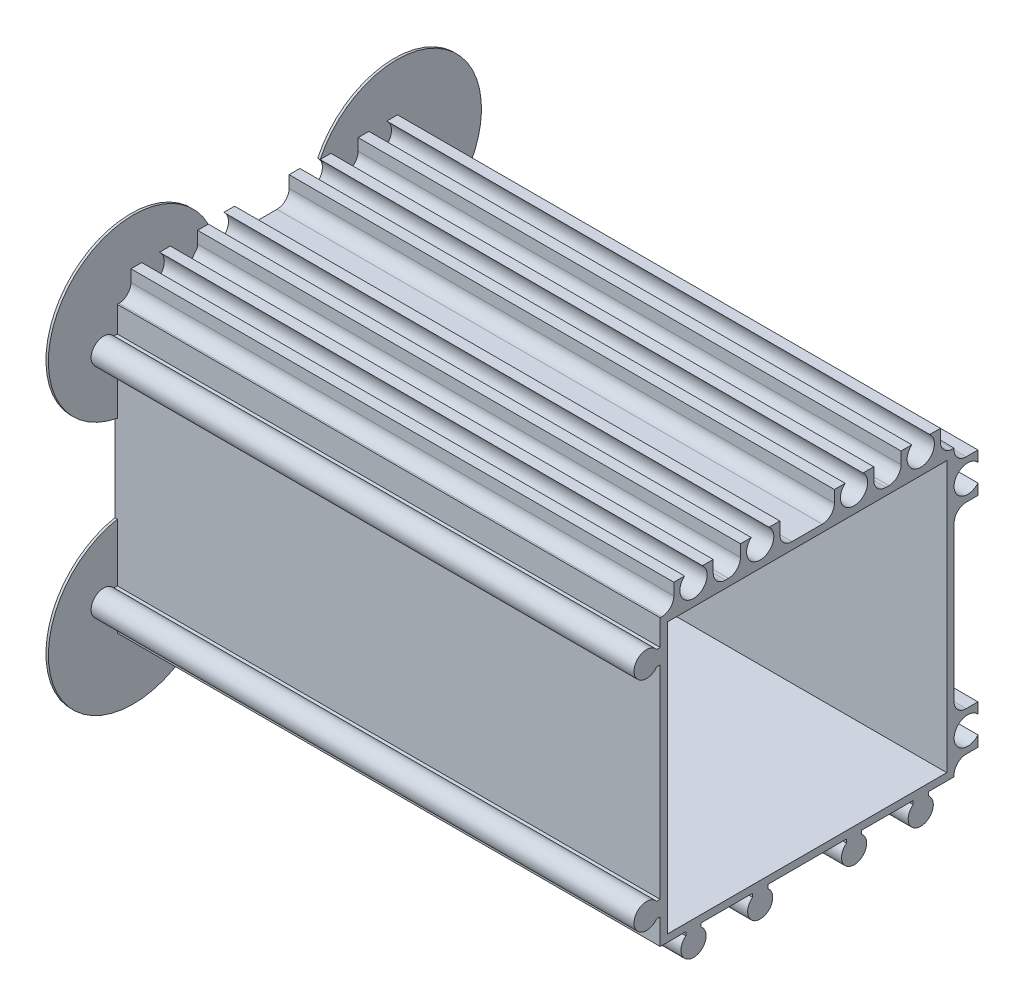
SolidWorks part; units mm, degrees
ref_plane "Спереди" through (0, 0, 0) normal (0, 0, 1) x (1, 0, 0)
ref_plane "Сверху" through (0, 0, 0) normal (0, 1, 0) x (1, 0, 0)
ref_plane "Справа" through (0, 0, 0) normal (1, 0, 0) x (0, 0, -1)
ref_plane "Плоскость4" through (90, 0, 0) normal (1, 0, 0) x (0, 0, -1)
sketch "Эскиз1" plane through (90, 0, 0) normal (1, 0, 0) x (0, 0, -1)
  line L0 (6.75, 160.9062) -> (6.75, 204.25)
  line L1 (6.75, 204.25) -> (-38.0938, 204.25)
  line L2 (-38.0938, 201.75) -> (-37.5, 201.75)
  line L3 (-37.5, 201.75) -> (-37.5, 168.25)
  line L4 (-37.5, 168.25) -> (-38.0938, 168.25)
  line L5 (-38.0938, 165.75) -> (-37.5, 165.75)
  line L6 (-37.5, 165.75) -> (-37.5, 161.5)
  line L7 (-37.5, 161.5) -> (-33.25, 161.5)
  line L8 (-33.25, 161.5) -> (-33.25, 160.9062)
  line L9 (-30.75, 160.9062) -> (-30.75, 161.5)
  line L10 (-30.75, 161.5) -> (-22.25, 161.5)
  line L11 (-22.25, 161.5) -> (-22.25, 160.9062)
  line L12 (-19.75, 160.9062) -> (-19.75, 161.5)
  line L13 (-19.75, 161.5) -> (-6.75, 161.5)
  line L14 (-6.75, 161.5) -> (-6.75, 160.9062)
  line L15 (-4.25, 160.9062) -> (-4.25, 161.5)
  line L16 (-4.25, 161.5) -> (4.25, 161.5)
  line L17 (4.25, 161.5) -> (4.25, 160.9062)
  arc A0 (-38.0938, 204.25) -> (-38.0938, 201.75) centre (-39.75, 203) ccw
  arc A1 (-38.0938, 168.25) -> (-38.0938, 165.75) centre (-39.75, 167) ccw
  arc A2 (-33.25, 160.9062) -> (-30.75, 160.9062) centre (-32, 159.25) ccw
  arc A3 (-22.25, 160.9062) -> (-19.75, 160.9062) centre (-21, 159.25) ccw
  arc A4 (-6.75, 160.9062) -> (-4.25, 160.9062) centre (-5.5, 159.25) ccw
  arc A5 (4.25, 160.9062) -> (6.75, 160.9062) centre (5.5, 159.25) ccw
extrude "Бобышка-Вытянуть1" add sketch "Эскиз1" against normal blind 90
sketch "Эскиз2" plane through (0, 0, -6.75) normal (0, 0, -1) x (-1, 0, 0)
  line L0 (0, 204.25) -> (0, 161.5)
  line L1 (0, 161.5) -> (-90, 161.5)
  line L2 (-90, 161.5) -> (-90, 204.25)
  line L3 (-90, 204.25) -> (0, 204.25)
extrude "Бобышка-Вытянуть2" add sketch "Эскиз2" along normal blind 8.2
sketch "Эскиз3" plane through (0, 204.25, 0) normal (0, 1, 0) x (-1, 0, 0)
  line L0 (-90, -14.95) -> (-90, 37.5)
  line L1 (-90, 37.5) -> (0, 37.5)
  line L2 (0, 37.5) -> (0, -14.95)
  line L3 (0, -14.95) -> (-90, -14.95)
extrude "Бобышка-Вытянуть3" add sketch "Эскиз3" along normal blind 8.2
sketch "Эскиз4" plane through (0, 0, 0) normal (-1, 0, 0) x (0, 0, 1)
  line L0 (-14.95, 161.5) -> (-11, 161.5)
  line L1 (-11, 161.5) -> (-11, 163.75)
  line L2 (-11, 163.75) -> (-14.95, 163.75)
  line L3 (-14.95, 163.75) -> (-14.95, 161.5)
extrude "Вырез-Вытянуть1" cut sketch "Эскиз4" against normal through all
sketch "Эскиз5" plane through (0, 0, 0) normal (-1, 0, 0) x (0, 0, 1)
  line L0 (-14.95, 170.25) -> (-11, 170.25)
  line L1 (-11, 170.25) -> (-11, 199.75)
  line L2 (-11, 199.75) -> (-14.95, 199.75)
  line L3 (-14.95, 199.75) -> (-14.95, 170.25)
extrude "Вырез-Вытянуть2" cut sketch "Эскиз5" against normal through all
sketch "Эскиз6" plane through (0, 0, 0) normal (-1, 0, 0) x (0, 0, 1)
  line L0 (-14.95, 212.45) -> (-14.95, 206.25)
  line L1 (-14.95, 206.25) -> (-11, 206.25)
  line L2 (-11, 206.25) -> (-11, 212.45)
  line L3 (-11, 212.45) -> (-14.95, 212.45)
extrude "Вырез-Вытянуть3" cut sketch "Эскиз6" against normal through all
sketch "Эскиз7" plane through (0, 0, 0) normal (-1, 0, 0) x (0, 0, 1)
  line L0 (-11, 212.45) -> (-11, 208.5)
  line L1 (-11, 208.5) -> (-8.75, 208.5)
  line L2 (-8.75, 208.5) -> (-8.75, 212.45)
  line L3 (-8.75, 212.45) -> (-11, 212.45)
extrude "Вырез-Вытянуть4" cut sketch "Эскиз7" against normal through all
sketch "Эскиз8" plane through (0, 0, 0) normal (-1, 0, 0) x (0, 0, 1)
  line L0 (-2.25, 212.45) -> (-2.25, 208.5)
  line L1 (-2.25, 208.5) -> (2.25, 208.5)
  line L2 (2.25, 208.5) -> (2.25, 212.45)
  line L3 (2.25, 212.45) -> (-2.25, 212.45)
extrude "Вырез-Вытянуть5" cut sketch "Эскиз8" against normal through all
sketch "Эскиз9" plane through (0, 0, 0) normal (-1, 0, 0) x (0, 0, 1)
  line L0 (8.75, 212.45) -> (8.75, 208.5)
  line L1 (8.75, 208.5) -> (17.75, 208.5)
  line L2 (17.75, 208.5) -> (17.75, 212.45)
  line L3 (17.75, 212.45) -> (8.75, 212.45)
extrude "Вырез-Вытянуть6" cut sketch "Эскиз9" against normal through all
sketch "Эскиз10" plane through (0, 0, 0) normal (-1, 0, 0) x (0, 0, 1)
  line L0 (24.25, 212.45) -> (24.25, 208.5)
  line L1 (24.25, 208.5) -> (28.75, 208.5)
  line L2 (28.75, 208.5) -> (28.75, 212.45)
  line L3 (28.75, 212.45) -> (24.25, 212.45)
extrude "Вырез-Вытянуть7" cut sketch "Эскиз10" against normal through all
sketch "Эскиз11" plane through (0, 0, 0) normal (-1, 0, 0) x (0, 0, 1)
  line L0 (37.5, 212.45) -> (35.25, 212.45)
  line L1 (35.25, 212.45) -> (35.25, 208.5)
  line L2 (35.25, 208.5) -> (37.5, 208.5)
  line L3 (37.5, 208.5) -> (37.5, 212.45)
extrude "Вырез-Вытянуть8" cut sketch "Эскиз11" against normal through all
sketch "Эскиз12" plane through (90, 0, 0) normal (1, 0, 0) x (0, 0, -1)
  line L0 (9.8, 207.3) -> (-36.3, 207.3)
  line L1 (-36.3, 207.3) -> (-36.3, 162.7)
  line L2 (-36.3, 162.7) -> (9.8, 162.7)
  line L3 (9.8, 162.7) -> (9.8, 207.3)
  line L4 (11, 170.25) -> (11, 199.75) construction
  line L5 (-37.5, 201.75) -> (-37.5, 168.25) construction
  line L6 (-8.75, 208.5) -> (-17.75, 208.5) construction
  line L7 (-19.75, 161.5) -> (-6.75, 161.5) construction
  dimension "D1" = 1.2
  dimension "D2" = 1.2
  dimension "D3" = 1.2
  dimension "D4" = 1.2
extrude "Вырез-Вытянуть9" cut sketch "Эскиз12" against normal blind 86.2
hole_wizard "Диаметр отверстия Ø2.5 (2.5)1" positions "Эскиз14" profile "Эскиз13" hole size "Ø2.5" standard "Ansi Metric"
sketch "Эскиз14" plane through (90, 0, 0) normal (1, 0, 0) x (0, 0, -1)
  point P0 (5.5, 159.25)
  point P1 (-21, 159.25)
  point P2 (-5.5, 159.25)
  point P3 (-32, 159.25)
  point P4 (-39.75, 167)
  point P5 (-39.75, 203)
sketch "Эскиз13" plane through (90, 159.25, -5.5) normal (0, 1, 0) x (0, 0, -1)
  line L0 (0, 0) -> (0, 90)
  line L1 (0, 90) -> (1.25, 90)
  line L2 (1.25, 90) -> (1.25, 0)
  line L5 (1.25, 0) -> (0, 0)
  line L11 (0, -6.35) -> (0, 107.95) construction
  dimension "Диаметр сквозного отверстия" = 2.5
  dimension "Глубина сквозного отверстия" = 90
hole_wizard "Диаметр отверстия Ø4.5 (4.5)1" positions "Эскиз16" profile "Эскиз15" hole size "Ø4.5" standard "Ansi Metric"
sketch "Эскиз16" plane through (0, 0, 0) normal (-1, 0, 0) x (0, 0, 1)
  point P0 (-13.25, 167)
  point P1 (-13.25, 203)
  point P2 (-5.5, 210.75)
  point P3 (5.5, 210.75)
  point P4 (21, 210.75)
  point P5 (32, 210.75)
sketch "Эскиз15" plane through (0, 167, -13.25) normal (0, 1, 0) x (0, 0, 1)
  line L0 (0, 0) -> (0, 90)
  line L1 (0, 90) -> (2.25, 90)
  line L2 (2.25, 90) -> (2.25, 0)
  line L5 (2.25, 0) -> (0, 0)
  line L11 (0, -6.35) -> (0, 107.95) construction
  dimension "Диаметр сквозного отверстия" = 4.5
  dimension "Глубина сквозного отверстия" = 90
hole_wizard "Диаметр отверстия Ø8.3 (8.3)1" [suppressed] positions "Эскиз18" profile "Эскиз17" hole size "Ø8.3" standard "Ansi Metric"
sketch "Эскиз18" plane through (0, 0, 0) normal (-1, 0, 0) x (0, 0, 1)
  point P0 (13.25, 185)
sketch "Эскиз17" plane through (0, 185, 13.25) normal (0, 1, 0) x (0, 0, 1)
  line L0 (0, 0) -> (0, 3.2)
  line L1 (0, 3.2) -> (4.15, 3.2)
  line L2 (4.15, 3.2) -> (4.15, 0)
  line L5 (4.15, 0) -> (0, 0)
  line L10 (0, 3.2) -> (-4.15, 3.2) construction
  line L11 (0, -6.35) -> (0, 107.95) construction
  dimension "Диаметр отверстия" = 8.3
  dimension "Глубина отверстия" = 3.2
  dimension "Угол заточки сверла" = 180
sketch "Эскиз19" plane through (90, 0, 0) normal (1, 0, 0) x (0, 0, -1)
  circle A0 centre (-39.75, 203) radius 1.6725
  circle A1 centre (-39.75, 167) radius 1.4592
  circle A2 centre (-32, 159.25) radius 1.4599
  circle A3 centre (-21, 159.25) radius 1.5928
  circle A4 centre (-5.5, 159.25) radius 1.5322
  circle A5 centre (5.5, 159.25) radius 1.5961
extrude "Бобышка-Вытянуть4" add sketch "Эскиз19" against normal blind 90
sketch "Эскиз20" [suppressed] plane through (0, 0, 0) normal (-1, 0, 0) x (0, 0, 1)
  circle A0 centre (13.25, 185) radius 4.15
extrude "Вырез-Вытянуть10" [suppressed] cut sketch "Эскиз20" against normal blind 90
fillet "Скругление1" radius 2 1 edges at (45, 208.5, -8.75)
fillet "Скругление2" radius 2 1 edges at (45, 163.75, -11)
fillet "Скругление3" radius 2 1 edges at (45, 170.25, -11)
fillet "Скругление4" radius 2 1 edges at (45, 199.75, -11)
fillet "Скругление5" radius 2 1 edges at (45, 206.25, -11)
fillet "Скругление6" radius 2 1 edges at (45, 208.5, -2.25)
fillet "Скругление7" radius 2 1 edges at (45, 208.5, 2.25)
fillet "Скругление8" radius 2 1 edges at (45, 208.5, 8.75)
fillet "Скругление9" radius 2 1 edges at (45, 208.5, 17.75)
fillet "Скругление10" radius 2 1 edges at (45, 208.5, 24.25)
fillet "Скругление11" radius 2 1 edges at (45, 208.5, 28.75)
fillet "Скругление12" radius 2 1 edges at (45, 208.5, 35.25)
sketch "Эскиз21" plane through (0, 0, 0) normal (-1, 0, 0) x (0, 0, 1)
  line L0 (37.5, 161.5) -> (-10.75, 208.5) construction
  line L1 (-11, 161.5) -> (37.5, 208.5) construction
  line L3 (-11, 172.25) -> (-11, 197.75) construction
  line L4 (37.5, 201.75) -> (37.5, 168.25) construction
  line L5 (13.375, 185) -> (37.5, 185) construction
  line L6 (-11, 192.6159) -> (4.0261, 212.45)
  line L7 (22.4739, 212.45) -> (37.5, 192.2073)
  line L8 (37.5, 177.7927) -> (22.4739, 157.55)
  line L9 (4.0261, 157.55) -> (-11, 177.3841)
  arc A0 (4.0261, 212.45) -> (-11, 192.6159) centre (-8.6036, 206.4092) ccw
  arc A1 (37.5, 192.2073) -> (22.4739, 212.45) centre (34.8786, 205.9597) ccw
  arc A2 (37.5, 177.7927) -> (22.4739, 157.55) centre (34.8786, 164.0403) cw
  arc A3 (4.0261, 157.55) -> (-11, 177.3841) centre (-8.6036, 163.5908) cw
  dimension "D1" = 14
  dimension "D2" = 14
extrude "Бобышка-Вытянуть5" add sketch "Эскиз21" against normal blind 0.4
equation "\"D2@Эскиз12\"=\"D1@Эскиз12\""
equation "\"D3@Эскиз12\"=\"D1@Эскиз12\""
equation "\"D4@Эскиз12\"=\"D1@Эскиз12\""
